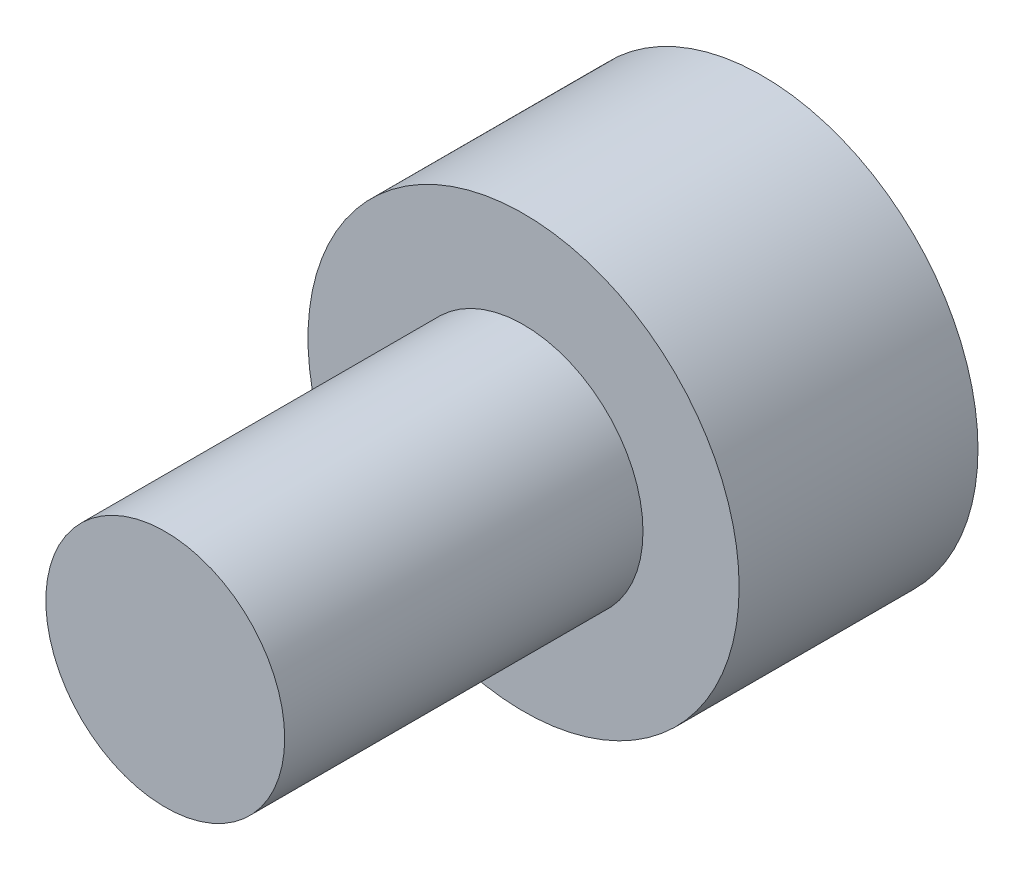
SolidWorks part; units mm, degrees
ref_plane "Front Plane" through (0, 0, 0) normal (0, 0, 1) x (1, 0, 0)
ref_plane "Top Plane" through (0, 0, 0) normal (0, 1, 0) x (1, 0, 0)
ref_plane "Right Plane" through (0, 0, 0) normal (1, 0, 0) x (0, 0, -1)
sketch "Sketch1" plane through (0, 0, 0) normal (0, 0, 1) x (1, 0, 0)
  circle A0 centre (0, 0) radius 3.61
  dimension "D1" = 7.22
extrude "Boss-Extrude1" add sketch "Sketch1" along normal blind 4
sketch "Sketch2" plane through (0, 0, 4) normal (0, 0, 1) x (1, 0, 0)
  circle A0 centre (0, 0) radius 2
  dimension "D1" = 4
extrude "Boss-Extrude2" add sketch "Sketch2" along normal blind 6
